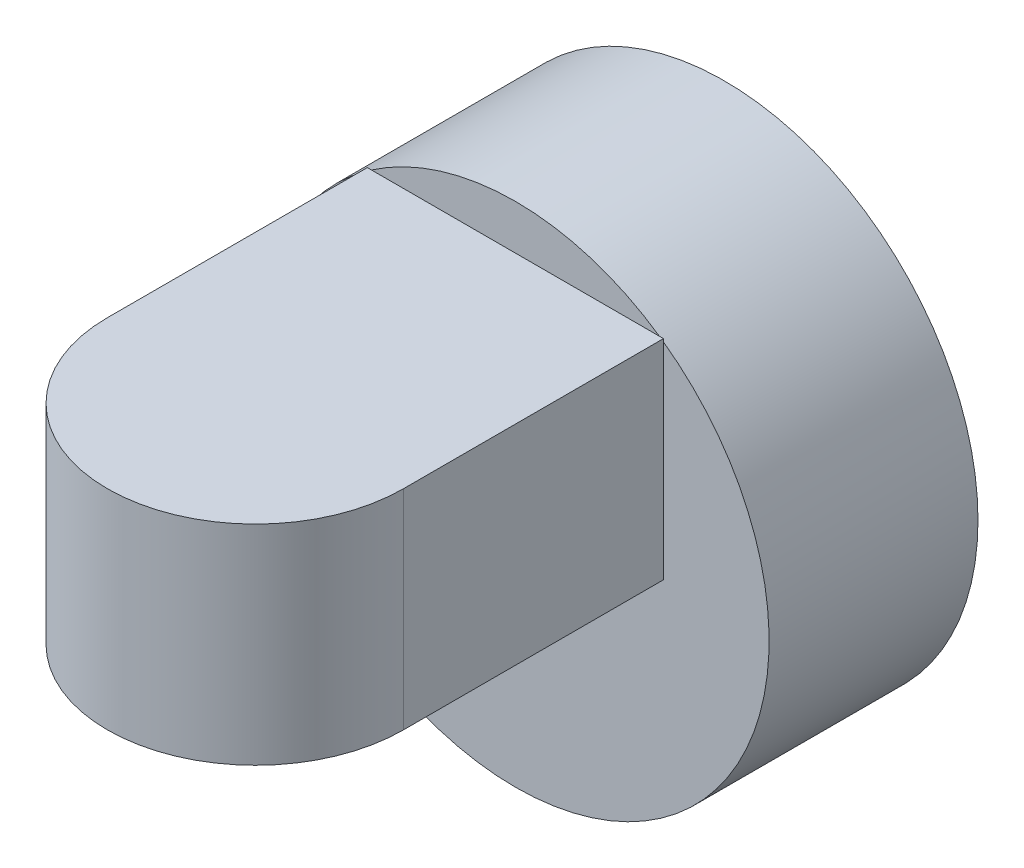
SolidWorks part; units mm, degrees
ref_plane "Front Plane" through (0, 0, 0) normal (0, 0, 1) x (1, 0, 0)
ref_plane "Top Plane" through (0, 0, 0) normal (0, 1, 0) x (1, 0, 0)
ref_plane "Right Plane" through (0, 0, 0) normal (1, 0, 0) x (0, 0, -1)
sketch "Sketch1" plane through (0, 0, 0) normal (0, 0, 1) x (1, 0, 0)
  circle A4 centre (0, 0) radius 12.85
  dimension "D1" = 25.7
extrude "Boss-Extrude5" add sketch "Sketch1" along normal blind 10.58
sketch "Sketch4" plane through (0, 0, 0) normal (0, 1, 0) x (1, 0, 0)
  line L0 (-7.5, -23.7493) -> (-7.5, -10.58)
  line L7 (-12.85, -10.58) -> (12.85, -10.58) construction
  line L8 (7.5, -23.7493) -> (7.5, -10.58)
  line L9 (-7.5, -10.58) -> (7.5, -10.58)
  circle A0 centre (0, -23.7493) radius 4.5
  circle A1 centre (0, -23.7493) radius 7.5
  dimension "D1" = 9
  dimension "D2" = 15
extrude "Boss-Extrude6" add sketch "Sketch4" along normal blind 10.58 contours A1 L8 L9 L0 | A1 A0 | A0
sketch "Sketch6" plane through (0, 0, 10.58) normal (0, 0, 1) x (1, 0, 0)
